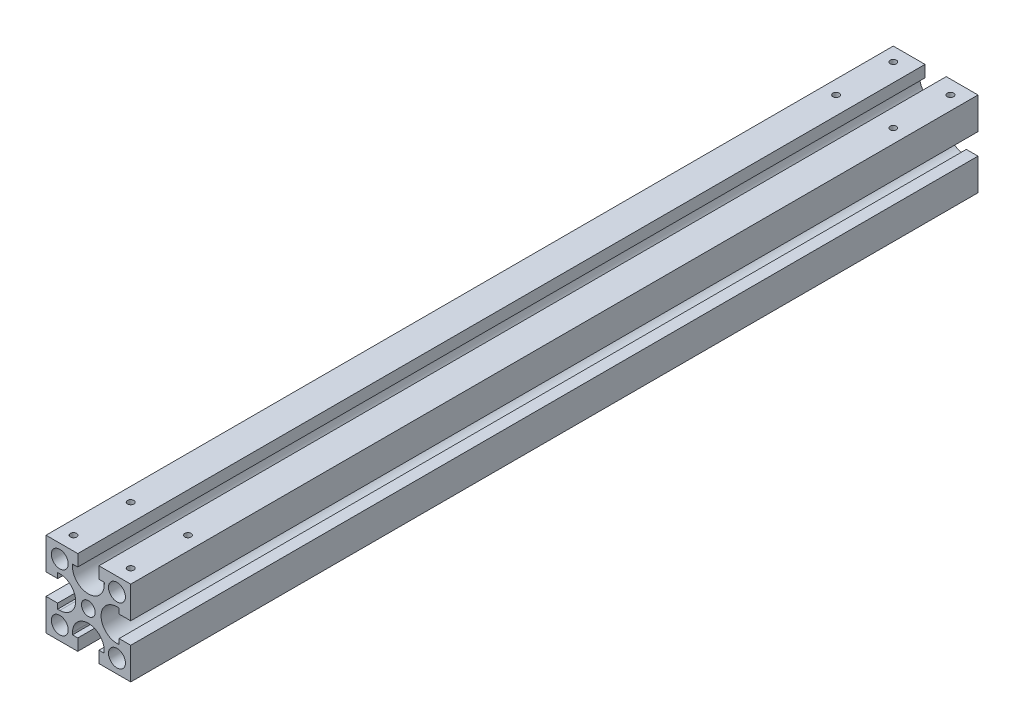
SolidWorks part; units mm, degrees
ref_plane "前基準面" through (0, 0, 0) normal (0, 0, 1) x (1, 0, 0)
ref_plane "上基準面" through (0, 0, 0) normal (0, 1, 0) x (1, 0, 0)
ref_plane "右基準面" through (0, 0, 0) normal (1, 0, 0) x (0, 0, -1)
sketch "草圖1" plane through (0, 0, 0) normal (0, 0, 1) x (1, 0, 0)
  line L0 (0, 20) -> (0, -20) construction
  line L1 (-20, -20) -> (20, -20)
  line L2 (-20, -20) -> (-20, 20)
  line L3 (-20, 20) -> (20, 20)
  line L4 (20, -20) -> (20, 20)
  dimension "D1" = 40
  dimension "D2" = 40
extrude "伸長1" add sketch "草圖1" along normal blind 400
sketch "草圖2" plane through (0, 0, 0) normal (0, 0, -1) x (-1, 0, 0)
  line L0 (-20, 20) -> (20, 20) construction
  line L4 (5, 14.5) -> (7.5, 14.5)
  line L5 (14.5, -5) -> (14.5, -7.5)
  line L6 (-5, 14.5) -> (-5, 20)
  line L7 (-5, 20) -> (5, 20)
  line L8 (5, 14.5) -> (5, 20)
  line L9 (14.5, 5) -> (20, 5)
  line L10 (-7.5, 13.5) -> (-7.5, 14.5)
  line L11 (-7.5, 14.5) -> (-5, 14.5)
  line L12 (7.5, 13.5) -> (7.5, 14.5)
  line L13 (20, 5) -> (20, -5)
  line L14 (14.5, -5) -> (20, -5)
  line L15 (13.5, 7.5) -> (14.5, 7.5)
  line L16 (14.5, 7.5) -> (14.5, 5)
  line L17 (13.5, -7.5) -> (14.5, -7.5)
  line L18 (-5, -14.5) -> (-7.5, -14.5)
  line L19 (5, -14.5) -> (5, -20)
  line L20 (5, -20) -> (-5, -20)
  line L21 (-5, -14.5) -> (-5, -20)
  line L22 (7.5, -13.5) -> (7.5, -14.5)
  line L23 (7.5, -14.5) -> (5, -14.5)
  line L24 (-7.5, -13.5) -> (-7.5, -14.5)
  line L25 (-14.5, 5) -> (-14.5, 7.5)
  line L26 (-14.5, -5) -> (-20, -5)
  line L27 (-20, -5) -> (-20, 5)
  line L28 (-14.5, 5) -> (-20, 5)
  line L29 (-13.5, -7.5) -> (-14.5, -7.5)
  line L30 (-14.5, -7.5) -> (-14.5, -5)
  line L31 (-13.5, 7.5) -> (-14.5, 7.5)
  line L32 (0, -20) -> (0, 0) construction
  line L33 (20, -20) -> (-20, -20) construction
  line L34 (0, 0) -> (-20, 0) construction
  line L35 (-20, -20) -> (-20, 20) construction
  line L36 (20, 20) -> (20, -20) construction
  circle A0 centre (0, 0) radius 3.25
  circle A1 centre (-13.5, 13.5) radius 4
  circle A2 centre (13.5, 13.5) radius 4
  circle A3 centre (-13.5, -13.5) radius 4
  circle A4 centre (13.5, -13.5) radius 4
  arc A5 (-7.5, 13.5) -> (7.5, 13.5) centre (0, 13.5) ccw
  arc A6 (13.5, 7.5) -> (13.5, -7.5) centre (13.5, 0) ccw
  arc A7 (7.5, -13.5) -> (-7.5, -13.5) centre (0, -13.5) ccw
  arc A8 (-13.5, -7.5) -> (-13.5, 7.5) centre (-13.5, 0) ccw
  dimension "D1" = 6.5
  dimension "D2" = 8
  dimension "D5" = 15
  dimension "D12" = 5.5
  dimension "D3" = 27
  dimension "D4" = 27
  dimension "D6" = 10
extrude "除料-伸長1" cut sketch "草圖2" against normal through all
hole_wizard "M3x0.5 螺紋孔2" positions "草圖7" profile "草圖6" tap size "M3x0.5" standard "JIS"
sketch "草圖7" plane through (0, 20, 0) normal (0, 1, 0) x (1, 0, 0)
  line L2 (-13.5, 0) -> (-13.5, -400) construction
  line L3 (-5, 0) -> (-20, 0) construction
  line L4 (-5, -400) -> (-20, -400) construction
  line L7 (0, -400) -> (0, 0) construction
  line L10 (-20, -400) -> (-20, 0) construction
  line L11 (13.5, 0) -> (13.5, -400) construction
  point P43 (-13.5, -6.5)
  point P45 (-13.5, -33.5)
  point P47 (-13.5, -393.5)
  point P49 (-13.5, -366.5)
  point P54 (13.5, -366.5)
  point P55 (13.5, -393.5)
  point P56 (13.5, -33.5)
  point P57 (13.5, -6.5)
  dimension "D1" = 6.5
  dimension "D2" = 6.5
  dimension "D3" = 27
  dimension "D4" = 6.5
  dimension "D5" = 27
sketch "草圖6" plane through (-13.5, 20, 6.5) normal (1, 0, 0) x (0, 0, 1)
  line L0 (0, 0) -> (0, 8.2511)
  line L1 (0, 8.2511) -> (1.25, 7.5)
  line L2 (1.25, 7.5) -> (1.25, 6)
  line L3 (1.25, 6) -> (1.5, 6)
  line L4 (1.5, 6) -> (1.5, 0)
  line L5 (1.5, 0) -> (0, 0)
  line L10 (0, 8.2511) -> (-1.25, 7.5) construction
  line L11 (0, -6.35) -> (0, 107.95) construction
  dimension "螺孔鑽直徑" = 2.5
  dimension "螺孔鑽深度" = 7.5
  dimension "螺紋主直徑" = 3
  dimension "螺紋深度" = 6
  dimension "導頭角度" = 118
